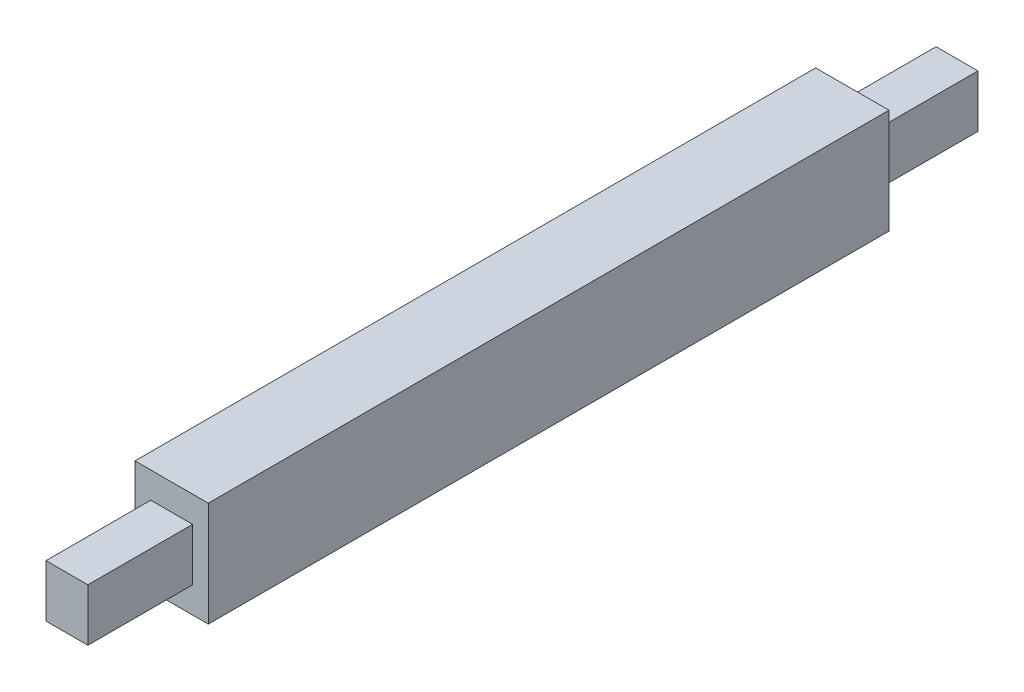
SolidWorks part; units mm, degrees
ref_plane "Front Plane" through (0, 0, 0) normal (0, 0, 1) x (1, 0, 0)
ref_plane "Top Plane" through (0, 0, 0) normal (0, 1, 0) x (1, 0, 0)
ref_plane "Right Plane" through (0, 0, 0) normal (1, 0, 0) x (0, 0, -1)
sketch "Sketch1" plane through (0, 0, 0) normal (0, 0, 1) x (1, 0, 0)
  line L1 (3.5, -5) -> (-3.5, -5)
  line L2 (3.5, -5) -> (3.5, 5)
  line L3 (3.5, 5) -> (-3.5, 5)
  line L4 (-3.5, -5) -> (-3.5, 5)
  line L5 (3.5, -5) -> (-3.5, 5) construction
  line L6 (3.5, 5) -> (-3.5, -5) construction
  point P0 (0, 0)
  dimension "D1" = 10
  dimension "D2" = 7
extrude "Boss-Extrude1" add sketch "Sketch1" along normal mid plane 65
sketch "Sketch2" plane through (0, 0, 32.5) normal (0, 0, 1) x (1, 0, 0)
  line L1 (2, -2.5) -> (-2, -2.5)
  line L2 (2, -2.5) -> (2, 2.5)
  line L3 (2, 2.5) -> (-2, 2.5)
  line L4 (-2, -2.5) -> (-2, 2.5)
  line L5 (2, -2.5) -> (-2, 2.5) construction
  line L6 (2, 2.5) -> (-2, -2.5) construction
  point P0 (0, 0)
  dimension "D1" = 5
  dimension "D2" = 4
extrude "Boss-Extrude2" add sketch "Sketch2" along normal blind 10
sketch "Sketch3" plane through (0, 0, -32.5) normal (0, 0, -1) x (-1, 0, 0)
  line L1 (2, -2.5) -> (-2, -2.5)
  line L2 (2, -2.5) -> (2, 2.5)
  line L3 (2, 2.5) -> (-2, 2.5)
  line L4 (-2, -2.5) -> (-2, 2.5)
  line L5 (2, -2.5) -> (-2, 2.5) construction
  line L6 (2, 2.5) -> (-2, -2.5) construction
  point P0 (0, 0)
  dimension "D1" = 5
  dimension "D2" = 4
extrude "Boss-Extrude3" add sketch "Sketch3" along normal blind 10
